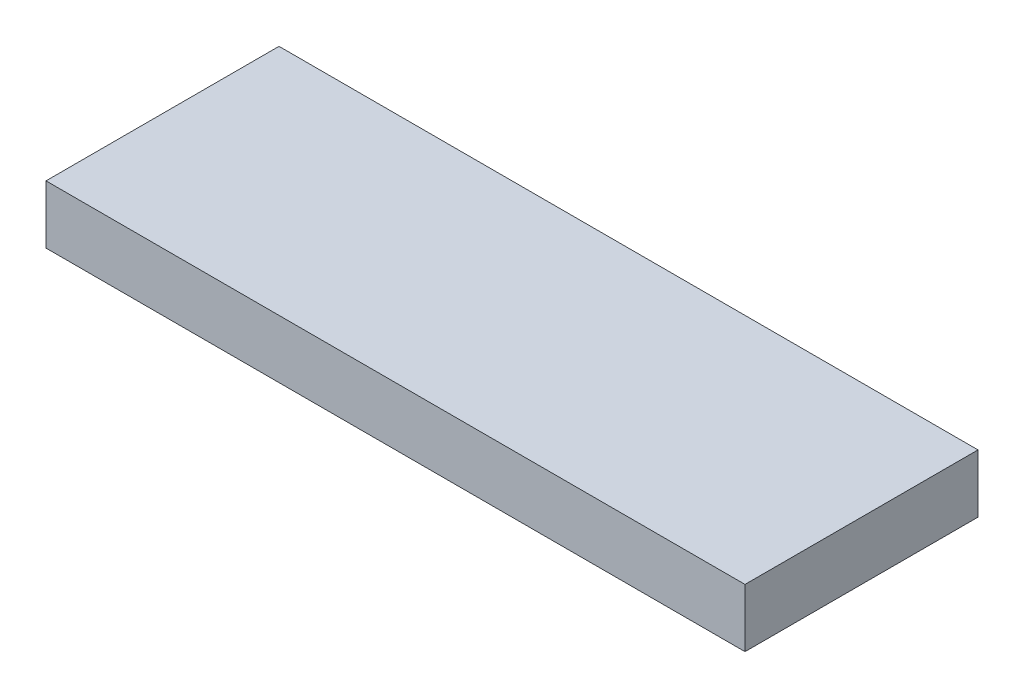
SolidWorks part; units mm, degrees
ref_plane "Front Plane" through (0, 0, 0) normal (0, 0, 1) x (1, 0, 0)
ref_plane "Top Plane" through (0, 0, 0) normal (0, 1, 0) x (1, 0, 0)
ref_plane "Right Plane" through (0, 0, 0) normal (1, 0, 0) x (0, 0, -1)
sketch "Sketch1" plane through (0, 0, 0) normal (0, 1, 0) x (1, 0, 0)
  line L1 (150, -50) -> (-150, -50)
  line L2 (150, -50) -> (150, 50)
  line L3 (150, 50) -> (-150, 50)
  line L4 (-150, -50) -> (-150, 50)
  line L5 (150, -50) -> (-150, 50) construction
  line L6 (150, 50) -> (-150, -50) construction
  point P0 (0, 0)
  dimension "D1" = 300
  dimension "D2" = 100
extrude "Boss-Extrude1" add sketch "Sketch1" along normal blind 25
